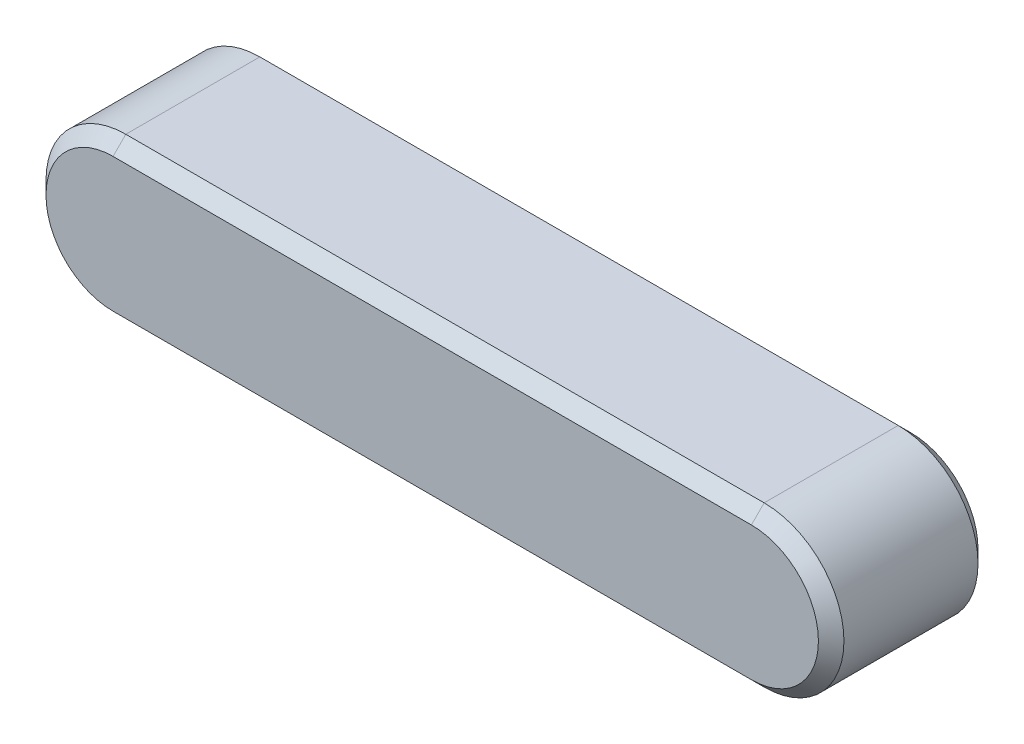
SolidWorks part; units mm, degrees
ref_plane "Front" through (0, 0, 0) normal (0, 0, 1) x (1, 0, 0)
ref_plane "Top" through (0, 0, 0) normal (0, 1, 0) x (1, 0, 0)
ref_plane "Right" through (0, 0, 0) normal (1, 0, 0) x (0, 0, -1)
sketch "Sketch1" plane through (0, 0, 0) normal (0, 0, 1) x (1, 0, 0)
  line L0 (-20, 2.5) -> (0, 2.5)
  line L1 (0, -2.5) -> (-20, -2.5)
  arc A0 (0, 2.5) -> (0, -2.5) centre (0, 0) cw
  arc A1 (-20, -2.5) -> (-20, 2.5) centre (-20, 0) cw
  dimension "L" = 25
  dimension "b" = 5
extrude "BaseKey" add sketch "Sketch1" along normal mid plane 5
sketch "Sketch2" plane through (0, 0, 0) normal (0, 0, 1) x (1, 0, 0)
  line L1 (-22.5, 2.5) -> (2.5, 2.5)
  line L2 (-22.5, 2.5) -> (-22.5, -2.5)
  line L3 (-22.5, -2.5) -> (2.5, -2.5)
  line L4 (2.5, 2.5) -> (2.5, -2.5)
  line L6 (0, -2.5) -> (-20, -2.5) construction
  line L7 (-20, 2.5) -> (0, 2.5) construction
  arc A2 (0, -2.5) -> (0, 2.5) centre (0, 0) ccw construction
  arc A3 (-20, 2.5) -> (-20, -2.5) centre (-20, 0) ccw construction
extrude "Extrude1" [suppressed] add sketch "Sketch2" along normal mid plane 5
sketch "Sketch3" plane through (0, 0, 0) normal (0, 0, 1) x (1, 0, 0)
  line L0 (2.5, 2.5) -> (-20, 2.5)
  line L1 (-20, -2.5) -> (2.5, -2.5)
  line L2 (2.5, -2.5) -> (2.5, 2.5)
  line L5 (-20, 2.5) -> (0, 2.5) construction
  arc A0 (-20, 2.5) -> (-20, -2.5) centre (-20, 0) ccw
  arc A1 (0, -2.5) -> (0, 2.5) centre (0, 0) ccw construction
  arc A4 (-20, 2.5) -> (-20, -2.5) centre (-20, 0) ccw construction
extrude "Extrude2" [suppressed] add sketch "Sketch3" along normal mid plane 5
chamfer "Chamfer1" distance 0.4 angle 45 8 edges at (2.5, 0, -2.5) (-10, -2.5, -2.5) (-22.5, 0, -2.5) (-10, 2.5, -2.5) (-22.5, 0, 2.5) (-10, -2.5, 2.5) (2.5, 0, 2.5) (-10, 2.5, 2.5)
equation "\"D1@Extrude1\"=\"h@BaseKey\""
equation "\"D1@Extrude2\"=\"h@BaseKey\""
